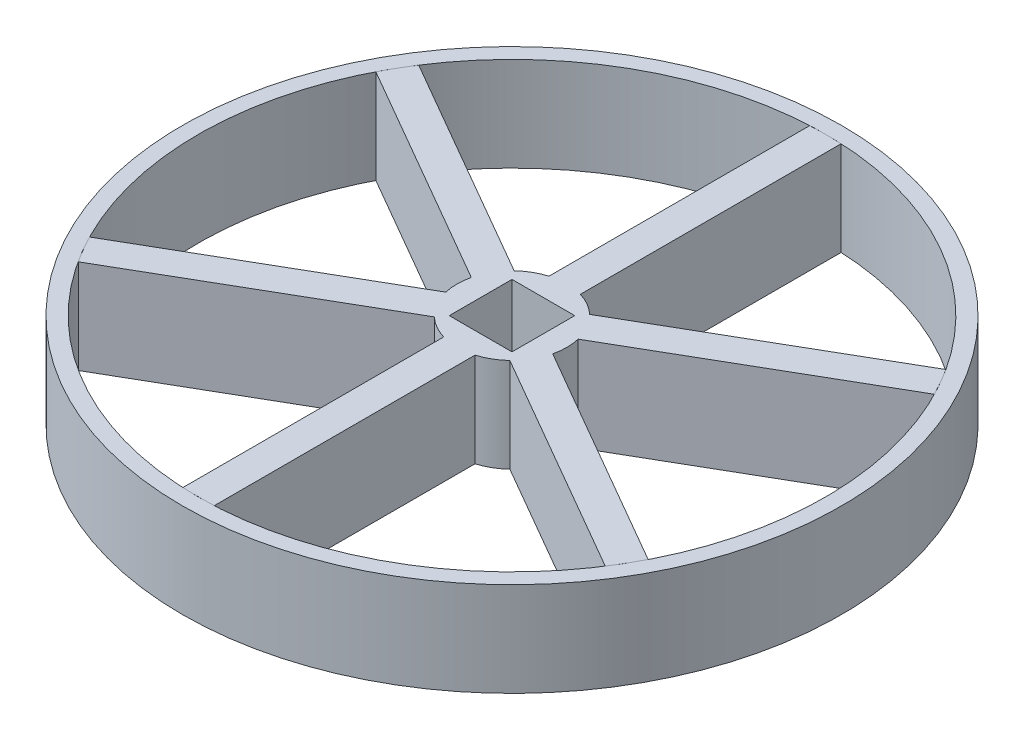
SolidWorks part; units mm, degrees
ref_plane "Front Plane" through (0, 0, 0) normal (0, 0, 1) x (1, 0, 0)
ref_plane "Top Plane" through (0, 0, 0) normal (0, 1, 0) x (1, 0, 0)
ref_plane "Right Plane" through (0, 0, 0) normal (1, 0, 0) x (0, 0, -1)
sketch "Sketch1" plane through (0, 0, 0) normal (0, 1, 0) x (1, 0, 0)
  circle A0 centre (0, 0) radius 20
  circle A1 centre (0, 0) radius 21
  dimension "D1" = 40
  dimension "D2" = 42
extrude "Boss-Extrude4" add sketch "Sketch1" along normal blind 6
sketch "Sketch4" plane through (0, 0, 0) normal (0, 1, 0) x (1, 0, 0)
  line L0 (0, -3.5) -> (0, -19.9934) construction
  line L1 (1, -3.3541) -> (1, -19.9683)
  line L2 (-1, -3.3541) -> (-1, -19.9683)
  line L3 (-1, -3.3541) -> (1, -3.3541)
  line L7 (-2.4047, -2.5431) -> (-16.7931, -10.8502)
  line L11 (-3.4047, -0.811) -> (-17.7931, -9.1181)
  line L15 (-3.4047, -0.811) -> (-2.4047, -2.5431)
  line L19 (-3.4047, 0.811) -> (-17.7931, 9.1181)
  line L23 (-2.4047, 2.5431) -> (-16.7931, 10.8502)
  line L27 (-2.4047, 2.5431) -> (-3.4047, 0.811)
  line L31 (-1, 3.3541) -> (-1, 19.9683)
  line L35 (1, 3.3541) -> (1, 19.9683)
  line L39 (1, 3.3541) -> (-1, 3.3541)
  line L43 (2.4047, 2.5431) -> (16.7931, 10.8502)
  line L47 (3.4047, 0.811) -> (17.7931, 9.1181)
  line L48 (2.4047, -2.5431) -> (16.7931, -10.8502) [skipped]
  line L49 (3.4047, -0.811) -> (17.7931, -9.1181) [skipped]
  line L50 (3.0311, -1.75) -> (17.3148, -9.9967) construction
  line L51 (3.3541, -1) -> (19.9683, -1) [skipped]
  line L52 (3.5, 0) -> (19.9934, 0) construction
  line L53 (3.3541, 1) -> (19.9683, 1) [skipped]
  line L54 (3.3541, -1) -> (3.3541, 1) [skipped]
  line L55 (2.4047, -2.5431) -> (3.4047, -0.811) [skipped]
  line L56 (2.4047, 2.5431) -> (16.7931, 10.8502) [skipped]
  line L57 (3.0311, 1.75) -> (17.3148, 9.9967) construction
  line L58 (3.4047, 0.811) -> (17.7931, 9.1181) [skipped]
  line L59 (3.4047, 0.811) -> (2.4047, 2.5431) [skipped]
  line L60 (2.5431, 2.4047) -> (10.8502, 16.7931) [skipped]
  line L61 (1.75, 3.0311) -> (9.9967, 17.3148) construction
  line L62 (0.811, 3.4047) -> (9.1181, 17.7931) [skipped]
  line L63 (2.5431, 2.4047) -> (0.811, 3.4047) [skipped]
  line L64 (-0.811, 3.4047) -> (-2.5431, 2.4047) [skipped]
  line L65 (-0.811, 3.4047) -> (-9.1181, 17.7931) [skipped]
  line L66 (-2.5431, 2.4047) -> (-10.8502, 16.7931) [skipped]
  line L67 (-1.75, 3.0311) -> (-9.9967, 17.3148) construction
  line L68 (-2.4047, 2.5431) -> (-16.7931, 10.8502) [skipped]
  line L69 (-3.4047, 0.811) -> (-17.7931, 9.1181) [skipped]
  line L70 (-3.0311, 1.75) -> (-17.3148, 9.9967) construction
  line L71 (-3.3541, 1) -> (-19.9683, 1) [skipped]
  line L72 (-3.3541, -1) -> (-19.9683, -1) [skipped]
  line L73 (-3.5, 0) -> (-19.9934, 0) construction
  line L74 (-3.4047, -0.811) -> (-17.7931, -9.1181) [skipped]
  line L75 (-2.4047, -2.5431) -> (-16.7931, -10.8502) [skipped]
  line L76 (-3.0311, -1.75) -> (-17.3148, -9.9967) construction
  line L77 (-2.5431, -2.4047) -> (-10.8502, -16.7931) [skipped]
  line L78 (-0.811, -3.4047) -> (-9.1181, -17.7931) [skipped]
  line L79 (-1.75, -3.0311) -> (-9.9967, -17.3148) construction
  line L80 (0.811, -3.4047) -> (9.1181, -17.7931) [skipped]
  line L81 (2.5431, -2.4047) -> (10.8502, -16.7931) [skipped]
  line L82 (1.75, -3.0311) -> (9.9967, -17.3148) construction
  line L83 (1, 3.3541) -> (1, 19.9683) [skipped]
  line L84 (-1, 3.3541) -> (-1, 19.9683) [skipped]
  line L85 (0, 3.5) -> (0, 19.9934) construction
  line L86 (0.811, -3.4047) -> (2.5431, -2.4047) [skipped]
  line L87 (1, 3.3541) -> (-1, 3.3541) [skipped]
  line L88 (-2.4047, 2.5431) -> (-3.4047, 0.811) [skipped]
  line L89 (-3.3541, 1) -> (-3.3541, -1) [skipped]
  line L90 (-3.4047, -0.811) -> (-2.4047, -2.5431) [skipped]
  line L91 (-2.5431, -2.4047) -> (-0.811, -3.4047) [skipped]
  line L92 (3.4047, 0.811) -> (2.4047, 2.5431)
  line L93 (3.4047, -0.811) -> (17.7931, -9.1181)
  line L94 (2.4047, -2.5431) -> (16.7931, -10.8502)
  line L95 (2.4047, -2.5431) -> (3.4047, -0.811)
  circle A0 centre (0, 0) radius 3.5
  arc A1 (-1, -19.9683) -> (1, -19.9683) centre (0, 0) ccw
  arc A2 (-10.8502, -16.7931) -> (-9.1181, -17.7931) centre (0, 0) ccw
  arc A3 (-17.7931, -9.1181) -> (-16.7931, -10.8502) centre (0, 0) ccw
  arc A4 (-19.9683, 1) -> (-19.9683, -1) centre (0, 0) ccw
  arc A5 (-16.7931, 10.8502) -> (-17.7931, 9.1181) centre (0, 0) ccw
  arc A7 (1, 19.9683) -> (-1, 19.9683) centre (0, 0) ccw
  arc A12 (9.1181, -17.7931) -> (10.8502, -16.7931) centre (0, 0) ccw
  arc A13 (19.9683, -1) -> (19.9683, 1) centre (0, 0) ccw [skipped]
  arc A14 (17.7931, 9.1181) -> (16.7931, 10.8502) centre (0, 0) ccw [skipped]
  arc A15 (10.8502, 16.7931) -> (9.1181, 17.7931) centre (0, 0) ccw [skipped]
  arc A16 (16.7931, -10.8502) -> (17.7931, -9.1181) centre (0, 0) ccw [skipped]
  arc A17 (-9.1181, 17.7931) -> (-10.8502, 16.7931) centre (0, 0) ccw [skipped]
  arc A18 (-17.7931, -9.1181) -> (-16.7931, -10.8502) centre (0, 0) ccw
  arc A19 (-16.7931, 10.8502) -> (-17.7931, 9.1181) centre (0, 0) ccw
  arc A20 (1, 19.9683) -> (-1, 19.9683) centre (0, 0) ccw
  arc A21 (17.7931, 9.1181) -> (16.7931, 10.8502) centre (0, 0) ccw
  arc A22 (16.7931, -10.8502) -> (17.7931, -9.1181) centre (0, 0) ccw
  point P40 (0, 0)
  point P78 (0, 0)
  dimension "D1" = 16.6142
  dimension "D6" = 6
  dimension "D2" = 1
  dimension "D3" = 1
  dimension "D4" = 12
  dimension "D5" = 2
extrude "Boss-Extrude5" add sketch "Sketch4" along normal blind 6 separate body
ref_plane "Plane1" through (0, 6, 0) normal (0, 1, 0) x (1, 0, 0)
sketch "Sketch5" plane through (0, 6, 0) normal (0, 1, 0) x (1, 0, 0)
  line L1 (-2, 2) -> (2, 2)
  line L2 (-2, 2) -> (-2, -2)
  line L3 (-2, -2) -> (2, -2)
  line L4 (2, 2) -> (2, -2)
  circle A0 centre (0, 0) radius 3.5 construction
  point P9 (-2, 0)
  point P11 (0, -2)
  dimension "D1" = 7
  dimension "D2" = 4
  dimension "D3" = 4
extrude "Cut-Extrude1" cut sketch "Sketch5" against normal blind 15
